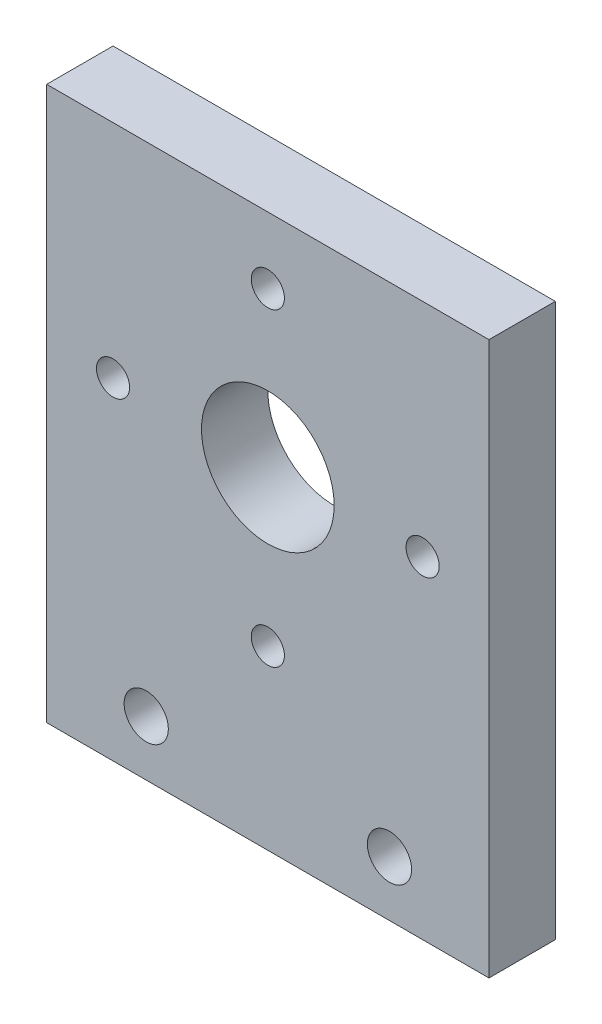
SolidWorks part; units mm, degrees
ref_plane "Front Plane" through (0, 0, 0) normal (0, 0, 1) x (1, 0, 0)
ref_plane "Top Plane" through (0, 0, 0) normal (0, 1, 0) x (1, 0, 0)
ref_plane "Right Plane" through (0, 0, 0) normal (1, 0, 0) x (0, 0, -1)
sketch "Sketch1" plane through (0, 0, 0) normal (0, 0, 1) x (1, 0, 0)
  line L0 (0, 0) -> (20, 0)
  line L1 (20, 0) -> (20, -20)
  line L2 (20, -20) -> (0, -20)
  line L3 (0, -20) -> (0, 0)
  line L4 (10, -10) -> (17, -10)
  line L5 (17, -10) -> (10, -10)
  line L6 (10, -10) -> (10, -3)
  line L7 (10, -10) -> (3, -10)
  line L8 (10, -10) -> (10, -17)
  line L9 (10, -20) -> (10, -22.5)
  line L10 (10, -22.5) -> (15.5, -22.5)
  line L11 (10, -22.5) -> (4.5, -22.5)
  line L12 (0, -20) -> (0, -25)
  line L13 (0, -25) -> (20, -25)
  line L14 (20, -25) -> (20, -20)
  circle A0 centre (10, -10) radius 3
  circle A1 centre (3, -10) radius 0.75
  circle A2 centre (10, -3) radius 0.75
  circle A3 centre (17, -10) radius 0.75
  circle A4 centre (10, -17) radius 0.75
  circle A5 centre (4.5, -22.5) radius 1
  circle A6 centre (15.5, -22.5) radius 1
extrude "Boss-Extrude1" add sketch "Sketch1" along normal blind 3
